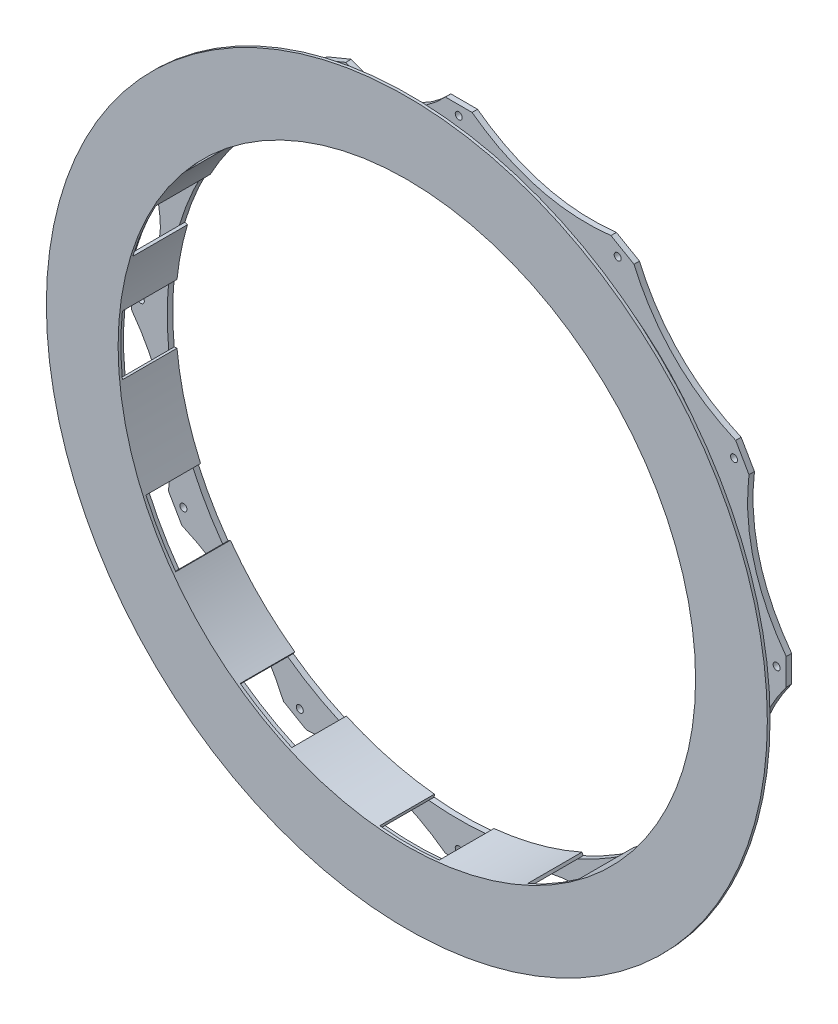
SolidWorks part; units mm, degrees
material "Maple"
ref_plane "Wasteboard" through (0, 0, 0) normal (0, 0, 1) x (1, 0, 0)
ref_plane "Left-Right" through (0, 0, 0) normal (0, 1, 0) x (1, 0, 0)
ref_plane "Front-Back" through (0, 0, 0) normal (1, 0, 0) x (0, 0, -1)
sketch "Sketch2" plane through (0, 0, 0) normal (0, 0, 1) x (1, 0, 0)
  line L0 (0, 0) -> (0, 50000) construction
  circle A0 centre (0, 0) radius 192.8812 construction
  circle A1 centre (0, 0) radius 209.55 construction
  circle A2 centre (0, 0) radius 172.72 construction
  circle A3 centre (0, 0) radius 252.73 construction
  circle A4 centre (0, 0) radius 184.785 construction
  circle A5 centre (0, 0) radius 190.5
  circle A6 centre (0, 0) radius 169.4688
  circle A7 centre (0, 0) radius 194.31 construction
  circle A8 centre (0, 184.785) radius 9.525 construction
  point P14 (0, 172.72)
  point P15 (0, 169.4688)
  point P16 (0, 175.26)
  dimension "D1" = 385.7625
  dimension "D2" = 419.1
  dimension "D3" = 2.54
  dimension "D4" = 505.46
  dimension "D5" = 369.57
  dimension "D6" = 381
  dimension "D7" = 3.2512
  dimension "D8" = 388.62
  dimension "D9" = 19.05
sketch "Sketch4" plane through (0, 0, 0) normal (0, 0, 1) x (1, 0, 0)
  line L0 (92.3925, 160.0285) -> (0, 184.785) construction
  line L1 (46.1963, 172.4068) -> (-12894.756, -48123.8846) construction
  line L2 (-7.7353, 190.3429) -> (7.7353, 190.3429)
  line L6 (-160.9741, -101.8704) -> (-168.7094, -88.4724)
  line L7 (-88.4724, -168.7094) -> (-101.8704, -160.9741)
  line L8 (7.7353, -190.3429) -> (-7.7353, -190.3429)
  line L9 (101.8704, -160.9741) -> (88.4724, -168.7094)
  line L10 (168.7094, -88.4724) -> (160.9741, -101.8704)
  line L11 (190.3429, 7.7353) -> (190.3429, -7.7353)
  line L12 (160.9741, 101.8704) -> (168.7094, 88.4724)
  line L13 (88.4724, 168.7094) -> (101.8704, 160.9741)
  line L14 (-101.8704, 160.9741) -> (-88.4724, 168.7094) [skipped]
  line L15 (-168.7094, 88.4724) -> (-160.9741, 101.8704) [skipped]
  line L16 (-79.9876, 172.8937) -> (-65.6945, 178.8141)
  line L17 (-70.7142, 170.7191) -> (0, 184.785) construction
  line L18 (-35.3571, 177.752) -> (9719.159, -48861.512) construction
  line L19 (-140.0625, 129.123) -> (-129.123, 140.0625)
  line L20 (-178.8141, 65.6945) -> (-172.8937, 79.9876)
  line L21 (-190.3429, -7.7353) -> (-190.3429, 7.7353)
  line L23 (-172.8937, -79.9876) -> (-178.8141, -65.6945) [skipped]
  line L24 (-190.3429, -7.7353) -> (-190.3429, 7.7353) [skipped]
  circle A0 centre (0, 184.785) radius 3.175 construction
  circle A1 centre (0, 184.785) radius 9.525 construction
  circle A2 centre (0, 184.785) radius 9.525 construction
  circle A3 centre (0, 0) radius 177.6413 construction
  circle A4 centre (0, 0) radius 190.5 construction
  circle A5 centre (0, 0) radius 184.785 construction
  circle A6 centre (0, 0) radius 169.4688 construction
  circle A7 centre (0, 0) radius 169.4688
  circle A8 centre (92.3925, 160.0285) radius 9.525 construction
  circle A9 centre (0, 0) radius 192.8812 construction
  circle A10 centre (0, 184.785) radius 2.032
  circle A14 centre (-160.0285, -92.3925) radius 2.032
  circle A15 centre (-92.3925, -160.0285) radius 2.032
  circle A16 centre (0, -184.785) radius 2.032
  circle A17 centre (92.3925, -160.0285) radius 2.032
  circle A18 centre (160.0285, -92.3925) radius 2.032
  circle A19 centre (184.785, 0) radius 2.032
  circle A20 centre (160.0285, 92.3925) radius 2.032
  circle A21 centre (92.3925, 160.0285) radius 2.032
  circle A22 centre (-160.0285, 92.3925) radius 2.032 [skipped]
  circle A23 centre (-92.3925, 160.0285) radius 2.032 [skipped]
  circle A24 centre (-70.7142, 170.7191) radius 9.525 construction
  circle A25 centre (-130.6627, 130.6627) radius 9.525 construction
  circle A26 centre (-170.7191, 70.7142) radius 9.525 construction
  circle A27 centre (-184.785, 0) radius 9.525 construction
  circle A28 centre (-70.7142, 170.7191) radius 2.032
  circle A29 centre (-130.6627, 130.6627) radius 2.032
  circle A30 centre (-170.7191, 70.7142) radius 2.032
  circle A31 centre (-184.785, 0) radius 2.032
  circle A32 centre (-184.785, 0) radius 2.032 [skipped]
  spline S0 degree 2 poles (7.7353, 190.3429) (43.85, 163.6504) (88.4724, 168.7094) knots 0 0 0 1 1 1
  spline S1 degree 2 poles (-65.6945, 178.8141) (-32.5972, 163.8774) (-7.7353, 190.3429) knots 0 0 0 1 1 1
  spline S2 degree 2 poles (-129.123, 140.0625) (-92.8291, 138.9285) (-79.9876, 172.8937) knots 0 0 0 1 1 1
  spline S3 degree 2 poles (-172.8937, 79.9876) (-138.9285, 92.8291) (-140.0625, 129.123) knots 0 0 0 1 1 1
  spline S4 degree 2 poles (-168.7094, -88.4724) (-163.6504, -43.85) (-190.3429, -7.7353) knots 0 0 0 1 1 1
  spline S5 degree 2 poles (-101.8704, -160.9741) (-119.8004, -119.8004) (-160.9741, -101.8704) knots 0 0 0 1 1 1
  spline S6 degree 2 poles (-7.7353, -190.3429) (-43.85, -163.6504) (-88.4724, -168.7094) knots 0 0 0 1 1 1
  spline S7 degree 2 poles (88.4724, -168.7094) (43.85, -163.6504) (7.7353, -190.3429) knots 0 0 0 1 1 1
  spline S8 degree 2 poles (160.9741, -101.8704) (119.8004, -119.8004) (101.8704, -160.9741) knots 0 0 0 1 1 1
  spline S9 degree 2 poles (190.3429, -7.7353) (163.6504, -43.85) (168.7094, -88.4724) knots 0 0 0 1 1 1
  spline S10 degree 2 poles (168.7094, 88.4724) (163.6504, 43.85) (190.3429, 7.7353) knots 0 0 0 1 1 1
  spline S11 degree 2 poles (101.8704, 160.9741) (119.8004, 119.8004) (160.9741, 101.8704) knots 0 0 0 1 1 1
  spline S12 degree 2 poles (-190.3429, 7.7353) (-163.8774, 32.5972) (-178.8141, 65.6945) knots 0 0 0 1 1 1
  point P6 (0, 0)
  point P18 (0, 0)
  point P19 (0, 0)
  point P21 (0, 0)
  point P24 (45.9769, 171.5883)
  point P29 (46.1963, 172.4068)
  point P31 (-7.7353, 190.3429)
  point P33 (-79.9876, 172.8937)
  point P34 (-65.6945, 178.8141)
  point P45 (0, 0)
  point P48 (-34.6561, 174.2279)
  point P103 (0, 0)
  point P112 (-35.3571, 177.752)
  point P123 (0, 0)
  point P126 (0, 0)
  dimension "D1" = 6.35
  dimension "D2" = 19.05
  dimension "D3" = 15.24
  dimension "D6" = 4.064
  dimension "D7" = 12
  dimension "D4" = 2
  dimension "D5" = 2
  dimension "D8" = 5
  dimension "D9" = 5
extrude "Boss-Extrude1" add sketch "Sketch4" along normal blind 3.175
ref_plane "Plane1" through (0, 0, 28.575) normal (0, 0, 1) x (1, 0, 0)
sketch "Sketch5" plane through (0, 0, 28.575) normal (0, 0, 1) x (1, 0, 0)
  line L13 (-129.123, 140.0625) -> (-140.0625, 129.123)
  line L14 (-65.6945, 178.8141) -> (-79.9876, 172.8937)
  line L15 (7.7353, 190.3429) -> (-7.7353, 190.3429)
  line L16 (101.8704, 160.9741) -> (88.4724, 168.7094)
  line L17 (168.7094, 88.4724) -> (160.9741, 101.8704)
  line L18 (190.3429, -7.7353) -> (190.3429, 7.7353)
  line L19 (160.9741, -101.8704) -> (168.7094, -88.4724)
  line L20 (88.4724, -168.7094) -> (101.8704, -160.9741)
  line L21 (-7.7353, -190.3429) -> (7.7353, -190.3429)
  line L22 (-101.8704, -160.9741) -> (-88.4724, -168.7094)
  line L23 (-168.7094, -88.4724) -> (-160.9741, -101.8704)
  line L24 (-190.3429, 7.7353) -> (-190.3429, -7.7353)
  line L25 (-172.8937, 79.9876) -> (-178.8141, 65.6945)
  line L26 (-129.123, 140.0625) -> (-140.0625, 129.123)
  line L27 (-65.6945, 178.8141) -> (-79.9876, 172.8937)
  line L28 (7.7353, 190.3429) -> (-7.7353, 190.3429)
  line L29 (101.8704, 160.9741) -> (88.4724, 168.7094)
  line L30 (168.7094, 88.4724) -> (160.9741, 101.8704)
  line L31 (190.3429, -7.7353) -> (190.3429, 7.7353)
  line L32 (160.9741, -101.8704) -> (168.7094, -88.4724)
  line L33 (88.4724, -168.7094) -> (101.8704, -160.9741)
  line L34 (-7.7353, -190.3429) -> (7.7353, -190.3429)
  line L35 (-101.8704, -160.9741) -> (-88.4724, -168.7094)
  line L36 (-168.7094, -88.4724) -> (-160.9741, -101.8704)
  line L37 (-190.3429, 7.7353) -> (-190.3429, -7.7353)
  line L38 (-172.8937, 79.9876) -> (-178.8141, 65.6945)
  circle A1 centre (0, 0) radius 169.4688
  circle A2 centre (0, 0) radius 169.4688
  circle A3 centre (0, 184.785) radius 2.032
  circle A4 centre (0, 184.785) radius 2.032
  circle A5 centre (-160.0285, -92.3925) radius 2.032
  circle A6 centre (-160.0285, -92.3925) radius 2.032
  circle A7 centre (-70.7142, 170.7191) radius 2.032
  circle A8 centre (-70.7142, 170.7191) radius 2.032
  circle A9 centre (92.3925, -160.0285) radius 2.032
  circle A10 centre (92.3925, -160.0285) radius 2.032
  circle A11 centre (0, -184.785) radius 2.032
  circle A12 centre (0, -184.785) radius 2.032
  circle A13 centre (-92.3925, -160.0285) radius 2.032
  circle A14 centre (-92.3925, -160.0285) radius 2.032
  circle A15 centre (184.785, 0) radius 2.032
  circle A16 centre (184.785, 0) radius 2.032
  circle A17 centre (160.0285, -92.3925) radius 2.032
  circle A18 centre (160.0285, -92.3925) radius 2.032
  circle A19 centre (92.3925, 160.0285) radius 2.032
  circle A20 centre (92.3925, 160.0285) radius 2.032
  circle A21 centre (160.0285, 92.3925) radius 2.032
  circle A22 centre (160.0285, 92.3925) radius 2.032
  circle A23 centre (-184.785, 0) radius 2.032
  circle A24 centre (-184.785, 0) radius 2.032
  circle A25 centre (-170.7191, 70.7142) radius 2.032
  circle A26 centre (-170.7191, 70.7142) radius 2.032
  circle A27 centre (-130.6627, 130.6627) radius 2.032
  circle A28 centre (-130.6627, 130.6627) radius 2.032
  parabola Q13 (-140.0625, 129.123) -> (-172.8937, 79.9876) focus (-164.8995, 110.1823) apex (-147.7033, 98.6922)
  parabola Q14 (-79.9876, 172.8937) -> (-129.123, 140.0625) focus (-110.1823, 164.8995) apex (-98.6922, 147.7033)
  parabola Q15 (-7.7353, 190.3429) -> (-65.6945, 178.8141) focus (-38.6909, 194.5123) apex (-34.6561, 174.2279)
  parabola Q16 (88.4724, 168.7094) -> (7.7353, 190.3429) focus (59.7292, 222.9123) apex (45.9769, 171.5883)
  parabola Q17 (160.9741, 101.8704) -> (101.8704, 160.9741) focus (163.1831, 163.1831) apex (125.6113, 125.6113)
  parabola Q18 (190.3429, 7.7353) -> (168.7094, 88.4724) focus (222.9123, 59.7292) apex (171.5883, 45.9769)
  parabola Q19 (168.7094, -88.4724) -> (190.3429, -7.7353) focus (222.9123, -59.7292) apex (171.5883, -45.9769)
  parabola Q20 (101.8704, -160.9741) -> (160.9741, -101.8704) focus (163.1831, -163.1831) apex (125.6113, -125.6113)
  parabola Q21 (7.7353, -190.3429) -> (88.4724, -168.7094) focus (59.7292, -222.9123) apex (45.9769, -171.5883)
  parabola Q22 (-88.4724, -168.7094) -> (-7.7353, -190.3429) focus (-59.7292, -222.9123) apex (-45.9769, -171.5883)
  parabola Q23 (-160.9741, -101.8704) -> (-101.8704, -160.9741) focus (-163.1831, -163.1831) apex (-125.6113, -125.6113)
  parabola Q24 (-190.3429, -7.7353) -> (-168.7094, -88.4724) focus (-222.9123, -59.7292) apex (-171.5883, -45.9769)
  parabola Q25 (-178.8141, 65.6945) -> (-190.3429, 7.7353) focus (-194.5123, 38.6909) apex (-174.2279, 34.6561)
  parabola Q26 (-140.0625, 129.123) -> (-172.8937, 79.9876) focus (-164.8995, 110.1823) apex (-147.7033, 98.6922)
  parabola Q27 (-79.9876, 172.8937) -> (-129.123, 140.0625) focus (-110.1823, 164.8995) apex (-98.6922, 147.7033)
  parabola Q28 (-7.7353, 190.3429) -> (-65.6945, 178.8141) focus (-38.6909, 194.5123) apex (-34.6561, 174.2279)
  parabola Q29 (88.4724, 168.7094) -> (7.7353, 190.3429) focus (59.7292, 222.9123) apex (45.9769, 171.5883)
  parabola Q30 (160.9741, 101.8704) -> (101.8704, 160.9741) focus (163.1831, 163.1831) apex (125.6113, 125.6113)
  parabola Q31 (190.3429, 7.7353) -> (168.7094, 88.4724) focus (222.9123, 59.7292) apex (171.5883, 45.9769)
  parabola Q32 (168.7094, -88.4724) -> (190.3429, -7.7353) focus (222.9123, -59.7292) apex (171.5883, -45.9769)
  parabola Q33 (101.8704, -160.9741) -> (160.9741, -101.8704) focus (163.1831, -163.1831) apex (125.6113, -125.6113)
  parabola Q34 (7.7353, -190.3429) -> (88.4724, -168.7094) focus (59.7292, -222.9123) apex (45.9769, -171.5883)
  parabola Q35 (-88.4724, -168.7094) -> (-7.7353, -190.3429) focus (-59.7292, -222.9123) apex (-45.9769, -171.5883)
  parabola Q36 (-160.9741, -101.8704) -> (-101.8704, -160.9741) focus (-163.1831, -163.1831) apex (-125.6113, -125.6113)
  parabola Q37 (-190.3429, -7.7353) -> (-168.7094, -88.4724) focus (-222.9123, -59.7292) apex (-171.5883, -45.9769)
  parabola Q38 (-178.8141, 65.6945) -> (-190.3429, 7.7353) focus (-194.5123, 38.6909) apex (-174.2279, 34.6561)
  dimension "D1" = 0
  dimension "D2" = 0
  dimension "D3" = 0
  dimension "D4" = 0
  dimension "D5" = 0
  dimension "D6" = 0
  dimension "D7" = 0
  dimension "D8" = 0
  dimension "D9" = 0
  dimension "D10" = 0
  dimension "D11" = 0
  dimension "D12" = 0
  dimension "D13" = 0
  dimension "D14" = 0
  dimension "D15" = 0
extrude "Boss-Extrude2" add sketch "Sketch5" along normal blind 3.175 separate body
sketch "Sketch6" plane through (0, 0, 31.75) normal (0, 0, 1) x (1, 0, 0)
  line L0 (0, 0) -> (5154.6392, 49733.5872) construction
  line L1 (0, 0) -> (20402.7451, 45647.8695) construction
  line L2 (17.471, 168.5658) -> (17.3034, 166.9489)
  line L3 (68.4892, 153.2337) -> (69.1526, 154.7178)
  line L4 (99.4133, 137.2468) -> (98.4596, 135.9303)
  line L5 (135.9303, 98.4596) -> (137.2468, 99.4133)
  line L6 (154.7178, 69.1526) -> (153.2337, 68.4892)
  line L7 (166.9489, 17.3034) -> (168.5658, 17.471)
  line L8 (168.5658, -17.471) -> (166.9489, -17.3034)
  line L9 (153.2337, -68.4892) -> (154.7178, -69.1526)
  line L10 (137.2468, -99.4133) -> (135.9303, -98.4596)
  line L11 (98.4596, -135.9303) -> (99.4133, -137.2468)
  line L12 (69.1526, -154.7178) -> (68.4892, -153.2337)
  line L39 (17.3034, -166.9489) -> (17.471, -168.5658)
  line L40 (-17.471, -168.5658) -> (-17.3034, -166.9489)
  line L41 (-68.4892, -153.2337) -> (-69.1526, -154.7178)
  line L42 (-99.4133, -137.2468) -> (-98.4596, -135.9303)
  line L43 (-135.9303, -98.4596) -> (-137.2468, -99.4133)
  line L44 (-154.7178, -69.1526) -> (-153.2337, -68.4892)
  line L45 (-166.9489, -17.3034) -> (-168.5658, -17.471)
  line L46 (0, 0) -> (68.4892, 153.2337) construction
  line L47 (0, 0) -> (135.9303, 98.4596) construction
  line L48 (0, 0) -> (-5154.6392, 49733.5872) construction
  line L49 (0, 0) -> (-14269.9542, 47920.4383) construction
  line L50 (-47.9023, 160.8624) -> (-48.3662, 162.4204)
  line L51 (-17.3034, 166.9489) -> (-17.471, 168.5658)
  line L52 (-105.8153, 130.2861) -> (-106.8402, 131.5479)
  line L53 (-79.8749, 147.6189) -> (-80.6485, 149.0487)
  line L54 (-147.6189, 79.8749) -> (-149.0487, 80.6485)
  line L55 (-130.2861, 105.8153) -> (-131.5479, 106.8402)
  line L56 (-166.9489, 17.3034) -> (-168.5658, 17.471)
  line L57 (-160.8624, 47.9023) -> (-162.4204, 48.3662)
  line L58 (0, 0) -> (-17.3034, 166.9489) construction
  line L59 (0, 0) -> (-79.8749, 147.6189) construction
  circle A0 centre (92.3925, 160.0285) radius 2.032 construction
  arc A1 (17.471, 168.5658) -> (69.1526, 154.7178) centre (0, 0) cw
  circle A2 centre (0, 0) radius 169.4688 construction
  arc A3 (17.3034, 166.9489) -> (68.4892, 153.2337) centre (0, 0) cw
  arc A4 (99.4133, 137.2468) -> (137.2468, 99.4133) centre (0, 0) cw
  arc A5 (98.4596, 135.9303) -> (135.9303, 98.4596) centre (0, 0) cw
  arc A6 (154.7178, 69.1526) -> (168.5658, 17.471) centre (0, 0) cw
  arc A7 (153.2337, 68.4892) -> (166.9489, 17.3034) centre (0, 0) cw
  arc A8 (168.5658, -17.471) -> (154.7178, -69.1526) centre (0, 0) cw
  arc A9 (166.9489, -17.3034) -> (153.2337, -68.4892) centre (0, 0) cw
  arc A10 (137.2468, -99.4133) -> (99.4133, -137.2468) centre (0, 0) cw
  arc A11 (135.9303, -98.4596) -> (98.4596, -135.9303) centre (0, 0) cw
  arc A12 (69.1526, -154.7178) -> (17.471, -168.5658) centre (0, 0) cw
  arc A13 (68.4892, -153.2337) -> (17.3034, -166.9489) centre (0, 0) cw
  arc A14 (-17.471, -168.5658) -> (-69.1526, -154.7178) centre (0, 0) cw
  arc A15 (-17.3034, -166.9489) -> (-68.4892, -153.2337) centre (0, 0) cw
  arc A16 (-99.4133, -137.2468) -> (-137.2468, -99.4133) centre (0, 0) cw
  arc A17 (-98.4596, -135.9303) -> (-135.9303, -98.4596) centre (0, 0) cw
  arc A18 (-154.7178, -69.1526) -> (-168.5658, -17.471) centre (0, 0) cw
  arc A19 (-153.2337, -68.4892) -> (-166.9489, -17.3034) centre (0, 0) cw
  circle A20 centre (-70.7142, 170.7191) radius 2.032 construction
  arc A21 (-48.3662, 162.4204) -> (-17.471, 168.5658) centre (0, 0) cw
  arc A22 (-47.9023, 160.8624) -> (-17.3034, 166.9489) centre (0, 0) cw
  arc A23 (-106.8402, 131.5479) -> (-80.6485, 149.0487) centre (0, 0) cw
  arc A24 (-105.8153, 130.2861) -> (-79.8749, 147.6189) centre (0, 0) cw
  arc A25 (-149.0487, 80.6485) -> (-131.5479, 106.8402) centre (0, 0) cw
  arc A26 (-147.6189, 79.8749) -> (-130.2861, 105.8153) centre (0, 0) cw
  arc A27 (-168.5658, 17.471) -> (-162.4204, 48.3662) centre (0, 0) cw
  arc A28 (-166.9489, 17.3034) -> (-160.8624, 47.9023) centre (0, 0) cw
  dimension "D3" = 19.05
  dimension "D7" = 19.05
  dimension "D2" = 19.05
  dimension "D4" = 1.6256
  dimension "D6" = 30
  dimension "D8" = 19.05
  dimension "D9" = 1.6256
  dimension "D11" = 22.5
  dimension "D5" = 9
  dimension "D10" = 4
extrude "Boss-Extrude3" add sketch "Sketch6" against normal through all
sketch "Sketch7" plane through (0, 0, 31.75) normal (0, 0, 1) x (1, 0, 0)
  circle A0 centre (0, 0) radius 167.8432
  circle A1 centre (0, 0) radius 209.55
  arc A2 (-166.9489, -17.3034) -> (-153.2337, -68.4892) centre (0, 0) ccw construction
  circle A5 centre (0, 0) radius 209.55 construction
  dimension "D1" = 41.7068
extrude "Boss-Extrude4" add sketch "Sketch7" along normal blind 1.5875
